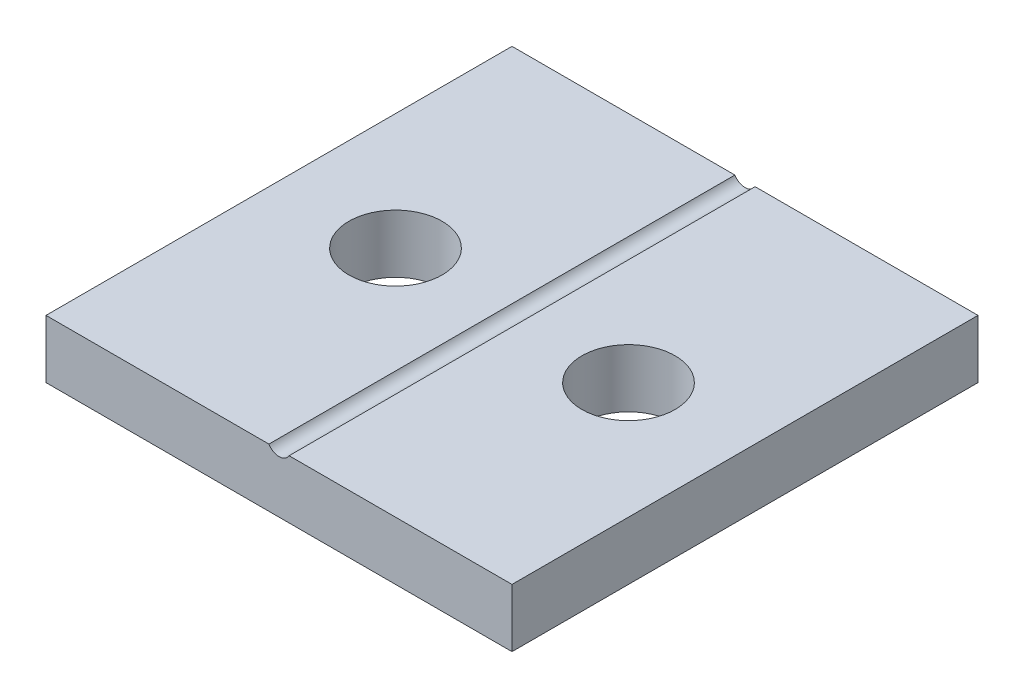
SolidWorks part; units mm, degrees
ref_plane "Front Plane" through (0, 0, 0) normal (0, 0, 1) x (1, 0, 0)
ref_plane "Top Plane" through (0, 0, 0) normal (0, 1, 0) x (1, 0, 0)
ref_plane "Right Plane" through (0, 0, 0) normal (1, 0, 0) x (0, 0, -1)
sketch "Sketch1" plane through (0, 0, 0) normal (0, 1, 0) x (1, 0, 0)
  line L1 (-60.7547, 52.0755) -> (-40.7547, 52.0755)
  line L2 (-60.7547, 52.0755) -> (-60.7547, 32.0755)
  line L3 (-60.7547, 32.0755) -> (-40.7547, 32.0755)
  line L4 (-40.7547, 52.0755) -> (-40.7547, 32.0755)
  dimension "D1" = 20
  dimension "D2" = 20
extrude "Boss-Extrude1" add sketch "Sketch1" along normal blind 2.5
sketch "Sketch2" plane through (0, 0, -32.0755) normal (0, 0, 1) x (1, 0, 0)
  line L0 (-60.7547, 2.5) -> (-40.7547, 2.5) construction
  line L1 (-50.7547, 6.7696) -> (-50.7547, 3.4135) construction
  circle A0 centre (-50.7547, 2.75) radius 0.5
  point P6 (-50.7547, 2.5)
  dimension "D2" = 1
  dimension "D1" = 0.25
extrude "Cut-Extrude1" cut sketch "Sketch2" against normal through all contours A0
sketch "Sketch3" plane through (0, 2.5, 0) normal (0, 1, 0) x (1, 0, 0)
  line L0 (-55.7547, 42.0755) -> (-45.7547, 42.0755) construction
  line L3 (-60.7547, 52.0755) -> (-40.7547, 32.0755) construction
  line L4 (-40.7547, 52.0755) -> (-60.7547, 32.0755) construction
  circle A0 centre (-55.7547, 42.0755) radius 2
  circle A1 centre (-45.7547, 42.0755) radius 2
  point P2 (-50.7547, 42.0755)
  dimension "D2" = 4
  dimension "D1" = 10
extrude "Cut-Extrude2" cut sketch "Sketch3" against normal through all
